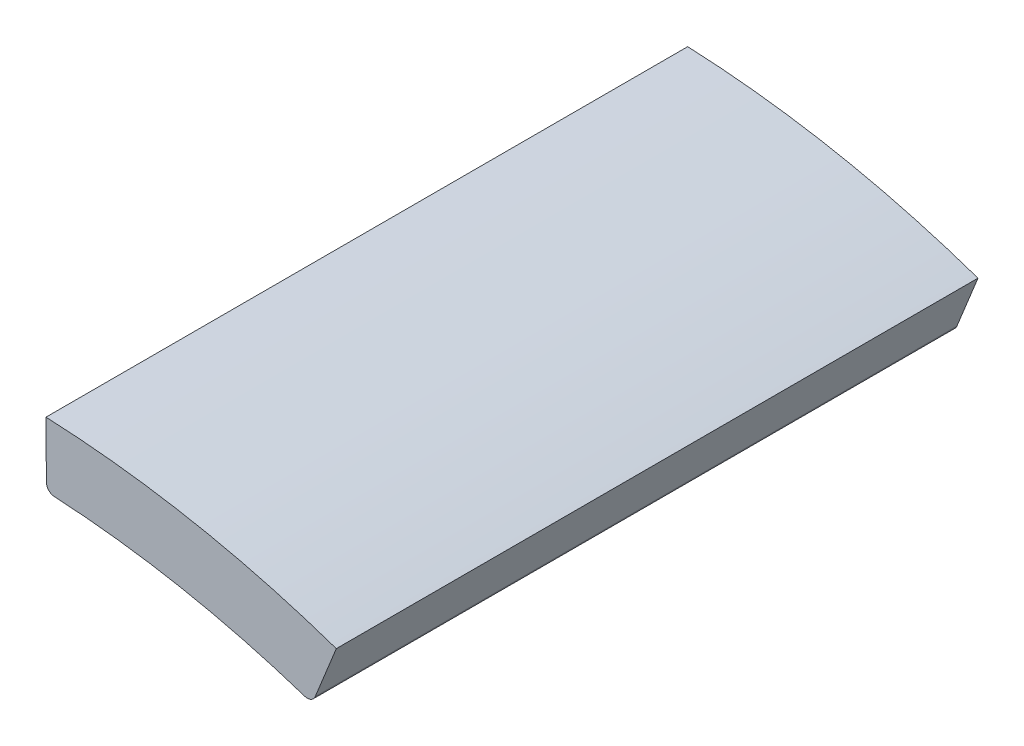
SolidWorks part; units mm, degrees
ref_plane "Front Plane" through (0, 0, 0) normal (0, 0, 1) x (1, 0, 0)
ref_plane "Top Plane" through (0, 0, 0) normal (0, 1, 0) x (1, 0, 0)
ref_plane "Right Plane" through (0, 0, 0) normal (1, 0, 0) x (0, 0, -1)
sketch "Sketch1" plane through (0, 0, 0) normal (0, 0, 1) x (1, 0, 0)
  line L2 (-99.1344, 21.7693) -> (-98.8171, 22.5532)
  line L3 (-105.5402, 23.8343) -> (-105.5334, 22.9886)
  line L4 (-105.531, 22.688) -> (-105.5334, 22.9886)
  line L5 (-99.2472, 21.4907) -> (-99.1344, 21.7693)
  line L6 (-105.5402, 23.8343) -> (-105.5402, 24.0017)
  line L7 (-98.8171, 22.5532) -> (-98.7543, 22.7085)
  arc A3 (-99.4957, 21.3759) -> (-99.2472, 21.4907) centre (-99.4326, 21.5657) ccw
  arc A4 (-105.531, 22.688) -> (-105.3422, 22.49) centre (-105.331, 22.6896) ccw
  arc A5 (-99.4957, 21.3759) -> (-105.3422, 22.49) centre (-106.5982, 0) ccw
  arc A8 (-82.5732, 0) -> (-130.6232, 0) centre (-106.5982, 0) ccw construction
  arc A9 (-105.5402, 24.0017) -> (-98.7543, 22.7085) centre (-106.5982, 0) cw
extrude "Boss-Extrude1" add sketch "Sketch1" against normal blind 15
